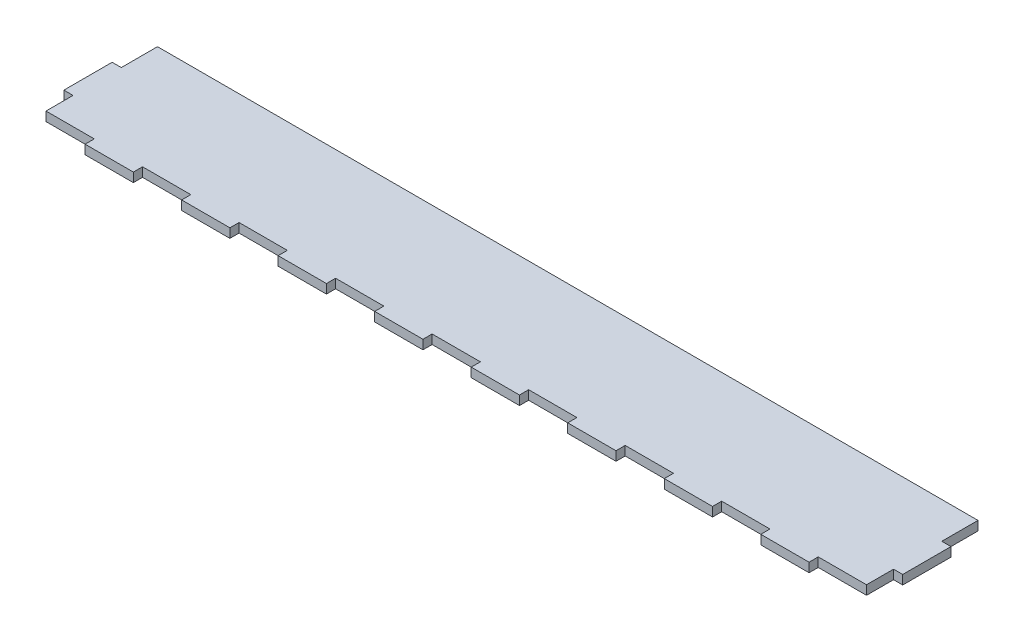
SolidWorks part; units mm, degrees
material "1060 Alloy"
ref_plane "Front Plane" through (0, 0, 0) normal (0, 0, 1) x (1, 0, 0)
ref_plane "Top Plane" through (0, 0, 0) normal (0, 1, 0) x (1, 0, 0)
ref_plane "Right Plane" through (0, 0, 0) normal (1, 0, 0) x (0, 0, -1)
sketch "Sketch2" plane through (0, 0, 0) normal (0, 1, 0) x (1, 0, 0)
  line L0 (146.05, 0) -> (146.05, 4.826)
  line L1 (0, 0) -> (622.3, 0) construction
  line L2 (0, 0) -> (0, 63.5) construction
  line L3 (0, 63.5) -> (622.3, 63.5) construction
  line L4 (622.3, 0) -> (622.3, 63.5) construction
  line L5 (95.25, 63.5) -> (527.05, 63.5)
  line L6 (95.25, 63.5) -> (95.25, 0)
  line L7 (95.25, 0) -> (527.05, 0)
  line L8 (527.05, 63.5) -> (527.05, 0)
  line L9 (95.25, 44.45) -> (90.424, 44.45)
  line L10 (95.25, 44.45) -> (95.25, 19.05)
  line L11 (95.25, 19.05) -> (90.424, 19.05)
  line L12 (90.424, 44.45) -> (90.424, 19.05)
  line L13 (527.05, 44.45) -> (531.876, 44.45)
  line L14 (527.05, 44.45) -> (527.05, 19.05)
  line L15 (527.05, 19.05) -> (531.876, 19.05)
  line L16 (531.876, 44.45) -> (531.876, 19.05)
  line L17 (95.25, 0) -> (120.65, 0)
  line L18 (95.25, 0) -> (95.25, 4.826)
  line L19 (95.25, 4.826) -> (120.65, 4.826)
  line L20 (120.65, 0) -> (120.65, 4.826)
  line L21 (146.05, 4.826) -> (171.45, 4.826)
  line L22 (171.45, 0) -> (171.45, 4.826)
  line L23 (196.85, 0) -> (196.85, 4.826)
  line L24 (196.85, 4.826) -> (222.25, 4.826)
  line L25 (222.25, 0) -> (222.25, 4.826)
  line L26 (247.65, 0) -> (247.65, 4.826)
  line L27 (247.65, 4.826) -> (273.05, 4.826)
  line L28 (273.05, 0) -> (273.05, 4.826)
  line L29 (298.45, 0) -> (298.45, 4.826)
  line L30 (298.45, 4.826) -> (323.85, 4.826)
  line L31 (323.85, 0) -> (323.85, 4.826)
  line L32 (349.25, 0) -> (349.25, 4.826)
  line L33 (349.25, 4.826) -> (374.65, 4.826)
  line L34 (374.65, 0) -> (374.65, 4.826)
  line L35 (400.05, 0) -> (400.05, 4.826)
  line L36 (400.05, 4.826) -> (425.45, 4.826)
  line L37 (425.45, 0) -> (425.45, 4.826)
  line L38 (450.85, 0) -> (450.85, 4.826)
  line L39 (450.85, 4.826) -> (476.25, 4.826)
  line L40 (476.25, 0) -> (476.25, 4.826)
  line L41 (501.65, 0) -> (501.65, 4.826)
  line L42 (501.65, 4.826) -> (527.05, 4.826)
  line L43 (527.05, 0) -> (527.05, 4.826)
  dimension "D1" = 622.3
  dimension "D2" = 63.5
  dimension "D3" = 95.25
  dimension "D4" = 95.25
  dimension "D5" = 4.826
  dimension "D6" = 25.4
  dimension "D7" = 19.05
  dimension "D8" = 25.4
  dimension "D9" = 4.826
  dimension "D10" = 19.05
  dimension "D12" = 25.4
  dimension "D13" = 4.826
  dimension "D14" = 9
extrude "Boss-Extrude1" add sketch "Sketch2" along normal blind 4.826 contours L40 L7 L8 L5 L6 L18 L19 L20 L0 L21 L22 L23 L24 L25 L26 L27 L28 L29 L30 L31 L32 L33 L34 L35 L36 L37 L38 L39 | L9 L12 L11 L6 | L16 L13 L8 L15
equation "\"sheet width\"= .19"
equation "\"width\"= 24.5"
equation "\"length\"= 34.5"
equation "\"standoff hole size\"= .5"
equation "\"ground clearence\"= 3"
equation "\"small drive pulley\"= 74.55mm"
equation "\"large drive pulley\"= 150.95mm"
equation "\"drive axle hole size\"= .5"
equation "\"front pulley clearence\"= 1"
equation "\"center support location\"= 19"
equation "\"inner to outer wall size\"= 3.75"
equation "\"D1@Sketch2\"=\"width\""
equation "\"D3@Sketch2\"=\"inner to outer wall size\""
equation "\"D4@Sketch2\"=\"inner to outer wall size\""
equation "\"D5@Sketch2\"=\"sheet width\""
equation "\"D9@Sketch2\"=\"sheet width\""
equation "\"D13@Sketch2\"=\"sheet width\""
equation "\"D1@Boss-Extrude1\"=\"sheet width\""
